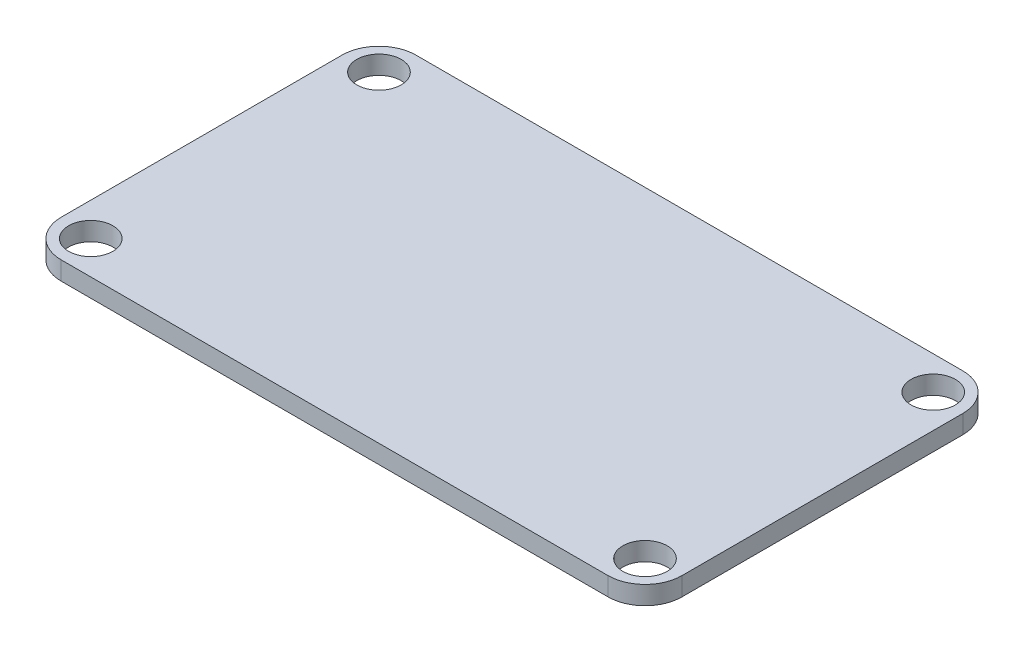
SolidWorks part; units mm, degrees
ref_plane "Front" through (0, 0, 0) normal (0, 0, 1) x (1, 0, 0)
ref_plane "Top" through (0, 0, 0) normal (0, 1, 0) x (1, 0, 0)
ref_plane "Right" through (0, 0, 0) normal (1, 0, 0) x (0, 0, -1)
sketch "Sketch1" plane through (0, 0, 0) normal (0, 1, 0) x (1, 0, 0)
  line L0 (0, 0) -> (2.8575, 2.8575) construction
  line L1 (3.175, 0) -> (50.165, 0)
  line L2 (0, 3.175) -> (0, 27.305)
  line L3 (3.175, 30.48) -> (50.165, 30.48)
  line L4 (53.34, 3.175) -> (53.34, 27.305)
  line L5 (2.8575, 2.8575) -> (50.4825, 27.6225) construction
  line L6 (50.4825, 27.6225) -> (53.34, 30.48) construction
  circle A0 centre (2.8575, 2.8575) radius 1.905
  circle A1 centre (2.8575, 27.6225) radius 1.905
  circle A2 centre (50.4825, 27.6225) radius 1.905
  circle A3 centre (50.4825, 2.8575) radius 1.905
  arc A4 (50.165, 30.48) -> (53.34, 27.305) centre (50.165, 27.305) cw
  arc A5 (50.165, 0) -> (53.34, 3.175) centre (50.165, 3.175) ccw
  arc A6 (3.175, 0) -> (0, 3.175) centre (3.175, 3.175) cw
  arc A7 (0, 27.305) -> (3.175, 30.48) centre (3.175, 27.305) cw
  dimension "D1" = 3.81
  dimension "D6" = 3.175
  dimension "D2" = 47.625
  dimension "D3" = 24.765
  dimension "D4" = 53.34
  dimension "D5" = 30.48
extrude "Boss-Extrude1" add sketch "Sketch1" along normal blind 1.5875
